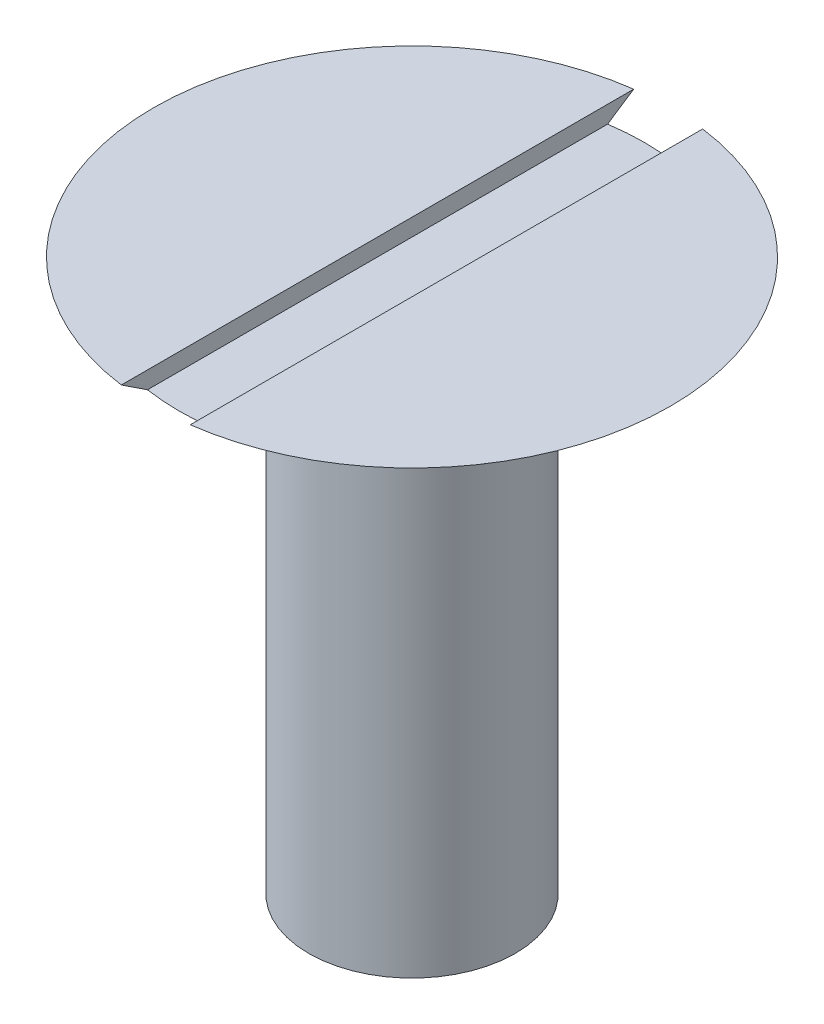
SolidWorks part; units mm, degrees
ref_plane "Front Plane" through (0, 0, 0) normal (0, 0, 1) x (1, 0, 0)
ref_plane "Top Plane" through (0, 0, 0) normal (0, 1, 0) x (1, 0, 0)
ref_plane "Right Plane" through (0, 0, 0) normal (1, 0, 0) x (0, 0, -1)
sketch "Sketch1" plane through (0, 0, 0) normal (0, 0, 1) x (1, 0, 0)
  line L0 (0, 0) -> (3, 1.7321)
  line L1 (3, 1.7321) -> (3, 14.7321)
  line L2 (3, 14.7321) -> (7.5, 17.7321)
  line L3 (7.5, 17.7321) -> (0, 17.7321)
  line L4 (0, 17.7321) -> (0, 0)
  dimension "D1" = 120
  dimension "D2" = 13
  dimension "D3" = 3
  dimension "D4" = 3
  dimension "D5" = 7.5
revolve "Revolve1" add sketch "Sketch1" angle 360 about L4
sketch "Sketch2" plane through (0, 0, 0) normal (0, 0, 1) x (1, 0, 0)
  line L0 (7.5, 17.7321) -> (-7.5, 17.7321) construction
  line L1 (-1, 17.2321) -> (1, 17.2321)
  line L2 (-1, 17.2321) -> (-1, 18.2321)
  line L3 (-1, 18.2321) -> (1, 18.2321)
  line L4 (1, 17.2321) -> (1, 18.2321)
  line L5 (-1, 17.2321) -> (1, 18.2321) construction
  line L6 (-1, 18.2321) -> (1, 17.2321) construction
  point P0 (0, 17.7321)
  dimension "D1" = 2
  dimension "D2" = 1
extrude "Cut-Extrude1" cut sketch "Sketch2" against normal through all both and the other way through all
